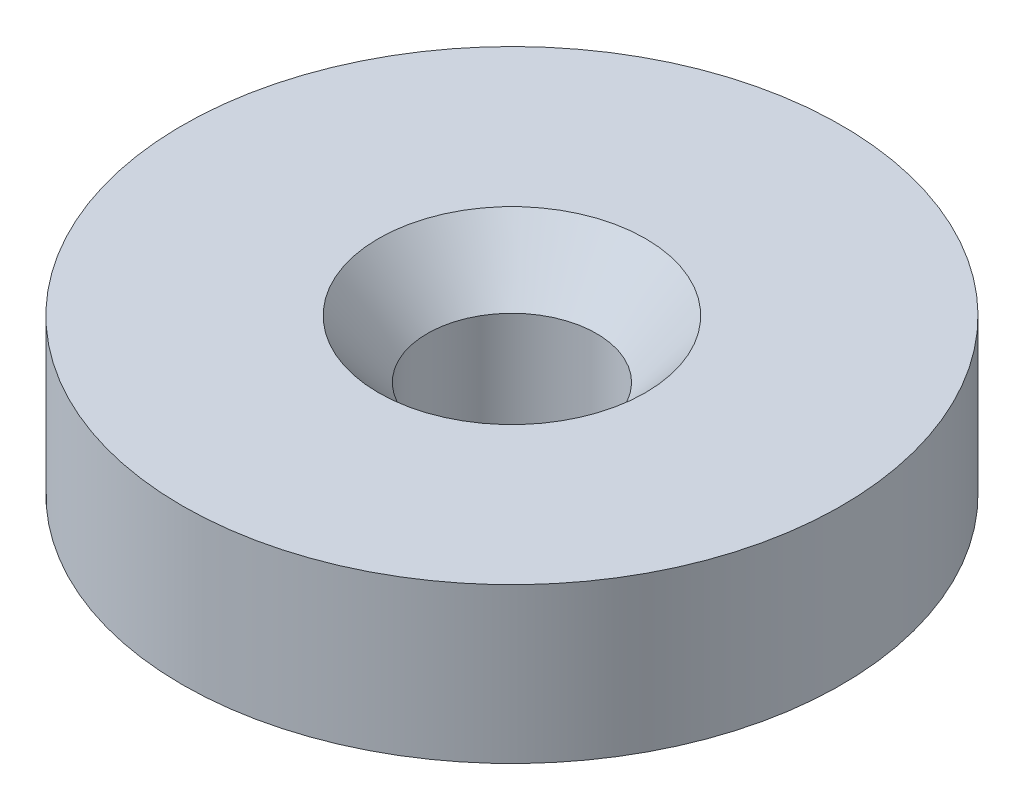
SolidWorks part; units mm, degrees
ref_plane "Спереди" through (0, 0, 0) normal (0, 0, 1) x (1, 0, 0)
ref_plane "Сверху" through (0, 0, 0) normal (0, 1, 0) x (1, 0, 0)
ref_plane "Справа" through (0, 0, 0) normal (1, 0, 0) x (0, 0, -1)
sketch "Эскиз1" plane through (0, 0, 0) normal (1, 0, 0) x (0, 0, -1)
  line L0 (0, 28.9073) -> (0, -17.1608) construction
  line L1 (2.5677, 0) -> (10, 0)
  line L2 (10, 0) -> (10, 4.7)
  line L3 (10, 4.7) -> (4.0514, 4.7)
  line L4 (4.0514, 4.7) -> (2.5677, 2.9465)
  line L5 (2.5677, 2.9465) -> (2.5677, 0)
  point P5 (0, 0)
  point P9 (0, 0)
  point P10 (0, 0)
  point P11 (5.2961, 6.1709)
  point P12 (2.5677, 2.9465)
  point P13 (0, 0)
revolve "Повернуть1" add sketch "Эскиз1" angle 360 about L0
